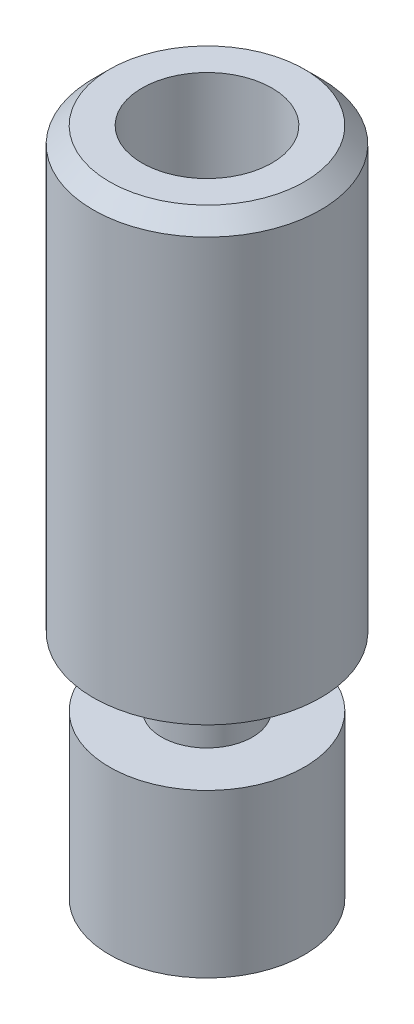
SolidWorks part; units mm, degrees
material "AISI 304"
ref_plane "Front Plane" through (0, 0, 0) normal (0, 0, 1) x (1, 0, 0)
ref_plane "Top Plane" through (0, 0, 0) normal (0, 1, 0) x (1, 0, 0)
ref_plane "Right Plane" through (0, 0, 0) normal (1, 0, 0) x (0, 0, -1)
sketch "Sketch1" plane through (0, 0, 0) normal (0, 0, 1) x (1, 0, 0)
  line L0 (0, -10.3) -> (0, 10.3) construction
  line L1 (1, -10.3) -> (3, -10.3)
  line L2 (3, -10.3) -> (3, -5.3)
  line L3 (3, -5.3) -> (1.4, -5.3)
  line L4 (1.4, -5.3) -> (1.4, -3.2)
  line L5 (1.4, -3.2) -> (3.5, -3.2)
  line L6 (3.5, -3.2) -> (3.5, 10.3)
  line L7 (3.5, 10.3) -> (2, 10.3)
  line L8 (2, 10.3) -> (2, 6.3)
  line L9 (2, 6.3) -> (1, 5.7226)
  line L10 (1, 5.7226) -> (1, -10.3)
  dimension "D1" = 20.6
  dimension "D2" = 2
  dimension "D3" = 6
  dimension "D4" = 2.8
  dimension "D5" = 7
  dimension "D6" = 4
  dimension "D7" = 4
  dimension "D8" = 13.5
  dimension "D9" = 2.1
  dimension "D10" = 120
revolve "Revolve1" add sketch "Sketch1" angle 360 about L0
chamfer "Chamfer1" distance 0.5 angle 45 1 edges at (0, 10.3, -3.5)
